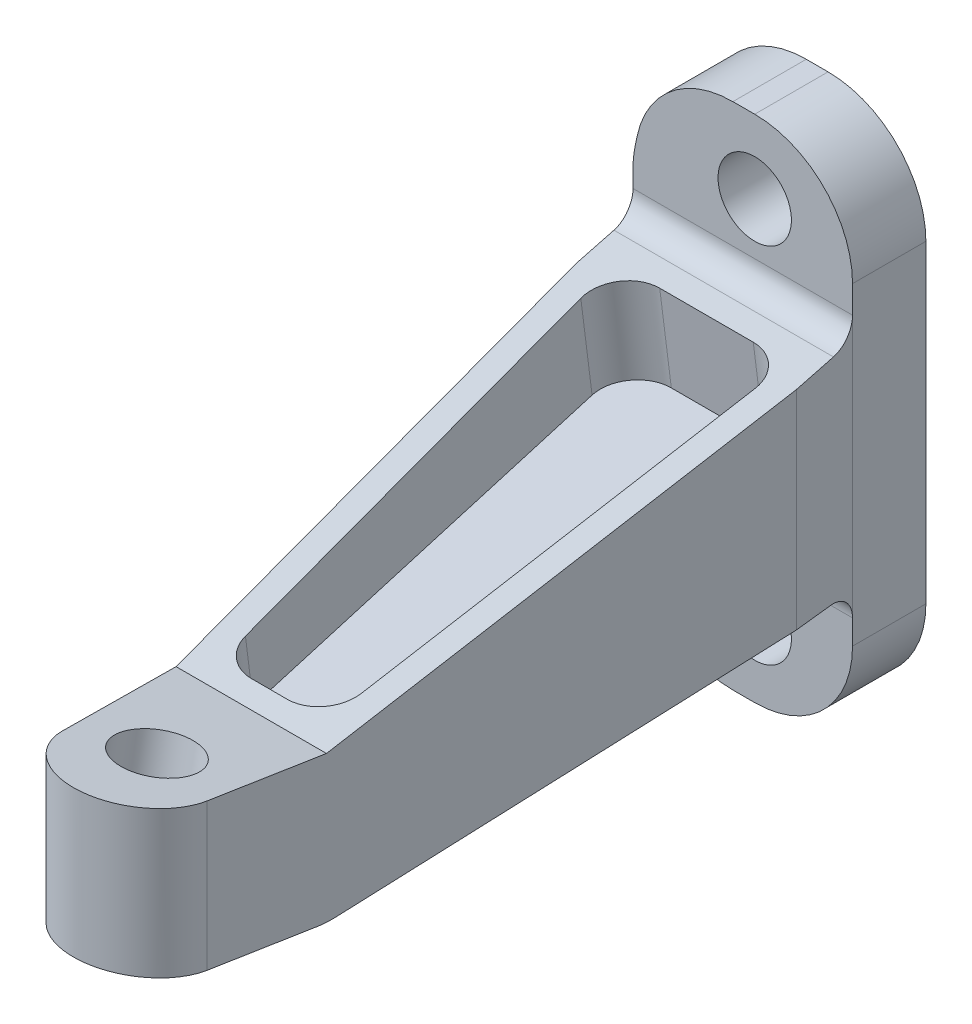
SolidWorks part; units mm, degrees
material "6061-T6 (SS)"
ref_plane "Front Plane" through (0, 0, 0) normal (0, 0, 1) x (1, 0, 0)
ref_plane "Top Plane" through (0, 0, 0) normal (0, 1, 0) x (1, 0, 0)
ref_plane "Right Plane" through (0, 0, 0) normal (1, 0, 0) x (0, 0, -1)
sketch "Sketch1" plane through (0, 0, 0) normal (0, 0, 1) x (1, 0, 0)
  line L8 (-28.5, -11.0464) -> (0, -11.0464)
  line L9 (-28.5, -17.3964) -> (-25.8774, -30.0964)
  line L10 (-25.8774, -30.0964) -> (0, -30.0964)
  line L11 (0, -30.0964) -> (0, 36.0645)
  line L12 (-28.5, 17.0145) -> (0, 17.0145)
  line L13 (-28.5, 23.3645) -> (-28.5, -17.3964)
  line L14 (-25.8774, 36.0645) -> (-28.5, 23.3645)
  line L15 (-25.8774, 36.0645) -> (0, 36.0645)
  circle A2 centre (-12.7, -20.5714) radius 4.7625
  circle A3 centre (-12.7, 26.5395) radius 4.7625
extrude "Boss-Extrude1" add sketch "Sketch1" along normal blind 9.525 contours L15 L14 L13 L12 L11 A3 | L8 L13 L9 L10 L11 A2 | L12 L13 L8 L11
sketch "Sketch2" plane through (0, 195.9337, -36.8296) normal (0, 0.9828, -0.1847) x (1, 0, 0)
  line L0 (71.608, 80.6018) -> (71.608, -49.3982) construction
  line L1 (71.608, 80.6018) -> (71.608, -49.3982)
  line L2 (71.608, 15.6018) -> (30.433, 15.6018)
  line L3 (30.433, -7.5988) -> (30.433, 15.6018)
  line L4 (30.433, 15.6018) -> (-5.144, -132.5874)
  dimension "D1" = 152.4
  dimension "D2" = 13.5
sketch "Sketch3" plane through (0, 0, 9.525) normal (0, 0, 1) x (1, 0, 0)
  line L0 (-28.5, -11.0464) -> (0, -11.0464) construction
  line L1 (-28.5, 17.0145) -> (0, 17.0145) construction
  line L2 (-28.5, -11.0464) -> (0, -11.0464)
  line L3 (-28.5, 17.0145) -> (0, 17.0145)
  line L4 (0, -30.0964) -> (0, 36.0645) construction
  line L5 (-28.5, 23.3645) -> (-28.5, -17.3964) construction
  line L6 (0, -11.0464) -> (0, 17.0145)
  line L7 (-28.5, 17.0145) -> (-28.5, -11.0464)
ref_plane "Plane1" through (0, -11.0464, 0) normal (0, 1, 0) x (1, 0, 0)
sketch "Sketch4" plane through (0, -11.0464, 0) normal (0, 1, 0) x (1, 0, 0)
  line L4 (-14.25, -9.525) -> (-5.144, -93.4757)
  line L5 (-5.144, -93.4757) -> (-3.7745, -106.1017)
  dimension "D1" = 12.7
sweep "Sweep1" add profiles "Sketch3" path "Sketch4"
sketch "Sketch5" plane through (0, 17.0145, 0) normal (0, 1, 0) x (1, 0, 0)
  line L0 (9.106, -93.4757) -> (-19.394, -93.4757) construction
  line L1 (-0.3815, -93.4757) -> (-19.394, -93.4757) construction
  circle A0 centre (-5.144, -93.4757) radius 4.7625
chamfer "Chamfer1" distance 88.9 angle 4 1 edges at (10.4755, 2.984, 106.1017)
chamfer "Chamfer2" distance 88.9 angle 4 1 edges at (-18.0245, 2.984, 106.1017)
fillet "Fillet1" radius 8.5286 4 edges at (-3.7271, 17.0145, 106.1017) (4.2696, 2.984, 106.1017) (-3.7271, -11.0464, 106.1017) (-11.7238, 2.984, 106.1017)
sketch "Sketch6" plane through (-28.5, 0, 0) normal (-1, 0, 0) x (0, 0, 1)
  line L0 (93.4757, -11.0464) -> (17.7201, -11.0464) construction
  line L1 (93.4757, -11.0464) -> (17.7201, -11.0464)
  line L3 (106.1017, 12.6977) -> (81.1392, 8.0036)
  line L6 (0, 23.3645) -> (0, -17.3964)
  line L7 (0, -17.3964) -> (9.525, -17.3964)
  line L8 (9.525, -17.3964) -> (9.525, -11.0464)
  line L9 (9.525, -11.0464) -> (9.525, 17.0145)
  line L11 (9.525, 23.3645) -> (0, 23.3645)
  line L12 (0, 23.3645) -> (0, -17.3964)
  line L13 (0, -17.3964) -> (9.525, -17.3964)
  line L14 (9.525, -17.3964) -> (9.525, -11.0464)
  line L15 (9.525, -11.0464) -> (9.525, 17.0145)
  line L17 (9.525, 23.3645) -> (0, 23.3645)
  line L20 (81.1392, -11.0464) -> (106.1017, -6.3523)
  line L21 (106.1017, -11.0464) -> (106.1017, 17.0145) construction
  line L22 (106.1017, -6.3523) -> (106.1017, 12.6977)
  line L25 (9.525, 17.0145) -> (17.7201, 36.9013)
  line L26 (17.7201, 36.9013) -> (128.3277, 30.3781)
  line L27 (128.3277, 30.3781) -> (117.9604, -22.8561)
  line L28 (117.9604, -22.8561) -> (81.1392, -11.0464)
  line L29 (81.1392, 8.0036) -> (9.525, 17.0145)
  line L35 (9.525, 17.0145) -> (9.525, 23.3645)
  line L36 (9.525, 17.0145) -> (9.525, 23.3645)
  dimension "D2" = 10.65
  dimension "D3" = 25.4
  dimension "D4" = 19.05
  dimension "D5" = 25.4
  dimension "D1" = 0
extrude "Cut-Extrude2" cut sketch "Sketch6" against normal through all
fillet "Fillet4" radius 3.175 2 edges at (-14.25, -11.0464, 9.525) (-14.25, 17.0145, 9.525)
sketch "Sketch8" plane through (0, 17.9291, 2.2559) normal (0, 0.9922, 0.1248) x (1, 0, 0)
  line L0 (-23.7948, -18.9006) -> (-14.2524, -72.404)
  line L1 (-9.5639, -76.3302) -> (-4.9297, -76.3302)
  line L2 (-0.1706, -71.3871) -> (-2.2012, -17.8838)
  line L3 (-2.2796, -15.8164) -> (-2.5503, -13.3019)
  line L4 (-6.9603, -13.3019) -> (-19.1063, -13.3019)
  line L5 (-24.6636, -13.3019) -> (-24.4661, -15.1369)
  arc A0 (-14.2524, -72.404) -> (-9.5639, -76.3302) centre (-9.5639, -71.5677) ccw
  arc A1 (-4.9297, -76.3302) -> (-0.1706, -71.3871) centre (-4.9297, -71.5677) ccw
  arc A2 (-23.7948, -18.9006) -> (-19.1063, -13.3019) centre (-19.1063, -18.0644) cw
  arc A3 (-6.9603, -13.3019) -> (-2.2012, -17.8838) centre (-6.9603, -18.0644) cw
  dimension "D3" = 4.7625
sketch "Sketch9" plane through (-28.5, 0, 0) normal (-1, 0, 0) x (0, 0, 1)
  line L0 (81.1392, -11.0464) -> (81.1392, 8.0036)
  line L1 (81.1392, 8.0036) -> (81.1392, -1.5214)
  line L2 (81.1392, -1.5214) -> (17.7201, 2.4684)
  line L3 (17.7201, -11.0464) -> (17.7201, 15.9833) construction
ref_plane "Plane3" through (0, 3.5691, 0.2245) normal (0, -0.998, -0.0628) x (-1, 0, 0)
extrude "Cut-Extrude3" cut sketch "Sketch8" against normal offset from surface (8.4408 mm away) 1.5875 contours A3 L4 A2 L0 A0 L1 A1 L2 up to plane "Plane3"
fillet "Fillet5" radius 12.7 1 edges at (-28.5, 23.3645, 4.7625)
fillet "Fillet6" radius 12.7 2 edges at (0, 36.0645, 4.7625) (-25.8774, 36.0645, 4.7625)
sketch "Sketch15" plane through (0, -7.0067, 1.3176) normal (0, 0.9828, -0.1848) x (1, 0, 0)
  circle A0 centre (-5.144, -95.01) radius 4.7625
extrude "Cut-Extrude7" cut sketch "Sketch15" against normal through all
fillet "Fillet9" radius 12.7 3 edges at (-28.5, -17.3964, 4.7625) (0, -30.0964, 4.7625) (-25.8774, -30.0964, 4.7625)
sketch "Sketch16" plane through (0, -11.0464, 0) normal (0, -1, 0) x (1, 0, 0)
  line L12 (-24.4666, 17.2675) -> (-24.6176, 15.875)
  line L13 (-24.6176, 15.875) -> (-2.5049, 15.875)
  line L14 (-2.5049, 15.875) -> (-2.2795, 17.9522)
  line L15 (-2.2795, 17.9522) -> (0.016, 77.9642)
  line L16 (0.016, 77.9642) -> (-13.5558, 77.9642)
  line L17 (-13.5558, 77.9642) -> (-24.4666, 17.2675)
  line L18 (-24.4666, 17.2675) -> (-24.6176, 15.875)
  line L19 (-19.0219, 15.875) -> (-6.9428, 15.875)
  line L20 (-2.5049, 15.875) -> (-2.2795, 17.9522)
  line L21 (-2.1838, 20.4555) -> (-0.1732, 73.0197)
  line L23 (-14.2605, 74.0443) -> (-23.7093, 21.4801)
  line L24 (-4.9322, 77.9642) -> (-9.5731, 77.9642)
  arc A0 (-19.0219, 15.875) -> (-23.7093, 21.4801) centre (-19.0219, 20.6375) cw
  arc A1 (-6.9428, 15.875) -> (-2.1838, 20.4555) centre (-6.9428, 20.6375) ccw
  arc A4 (-4.9322, 77.9642) -> (-0.1732, 73.0197) centre (-4.9322, 73.2017) cw
  arc A5 (-9.5731, 77.9642) -> (-14.2605, 74.0443) centre (-9.5731, 73.2017) ccw
  dimension "D2" = 4.7625
  dimension "D3" = 4.7625
  dimension "D1" = 3.175
extrude "Cut-Extrude8" cut sketch "Sketch16" against normal offset from surface (12.0403 mm away) 1.5875 contours L21 A4 L24 A5 L23 A0 L19 A1 up to plane "Plane3"
fillet "Fillet10" radius 12.7 1 edges at (-6.4481, -11.0464, 81.1392)
